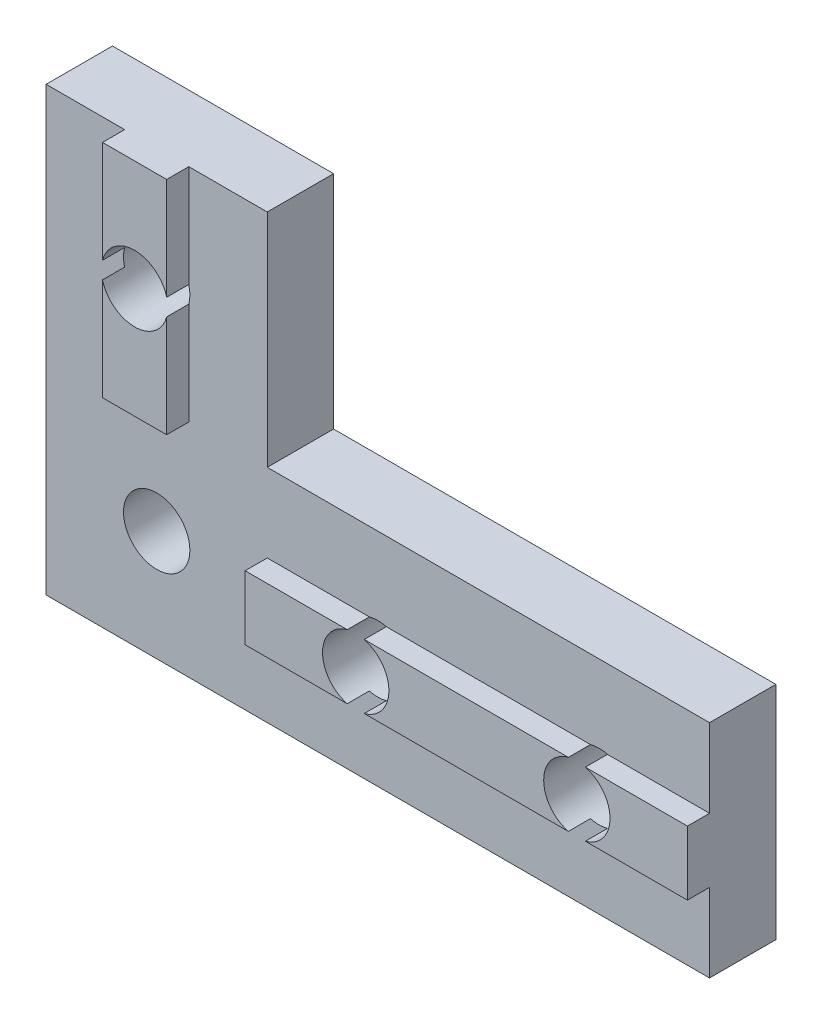
SolidWorks part; units mm, degrees
ref_plane "Front Plane" through (0, 0, 0) normal (0, 0, 1) x (1, 0, 0)
ref_plane "Top Plane" through (0, 0, 0) normal (0, 1, 0) x (1, 0, 0)
ref_plane "Right Plane" through (0, 0, 0) normal (1, 0, 0) x (0, 0, -1)
sketch "Esquisse1" plane through (0, 0, 0) normal (0, 0, 1) x (1, 0, 0)
  line L0 (0, 0) -> (30, 0)
  line L1 (30, 0) -> (30, 10)
  line L2 (30, 10) -> (10, 10)
  line L3 (10, 10) -> (10, 20)
  line L4 (10, 20) -> (0, 20)
  line L5 (0, 20) -> (0, 0)
  point P18 (5, 20)
  point P20 (30, 5)
  dimension "D2" = 20
  dimension "D1" = 10
  dimension "D8" = 30
extrude "Boss.-Extru.1" add sketch "Esquisse1" along normal blind 3
sketch "Esquisse2" plane through (0, 0, 3) normal (0, 0, 1) x (1, 0, 0)
  line L0 (10, 20) -> (0, 20) construction
  line L1 (6.45, 20) -> (3.55, 20)
  line L2 (6.45, 20) -> (6.45, 10)
  line L3 (6.45, 10) -> (3.55, 10)
  line L4 (3.55, 20) -> (3.55, 10)
  line L5 (30, 0) -> (30, 10) construction
  line L6 (30, 6.45) -> (10, 6.45)
  line L7 (30, 6.45) -> (30, 3.55)
  line L8 (30, 3.55) -> (10, 3.55)
  line L9 (10, 6.45) -> (10, 3.55)
  line L10 (30, 10) -> (10, 10) construction
  line L11 (10, 10) -> (10, 20) construction
  point P12 (5, 20)
  point P13 (5, 20)
  point P18 (30, 5)
  point P19 (30, 5)
  dimension "D1" = 2.9
extrude "Boss.-Extru.2" add sketch "Esquisse2" along normal blind 1
sketch "Esquisse3" plane through (0, 0, 0) normal (0, 0, -1) x (-1, 0, 0)
  line L0 (-10, 20) -> (0, 20) construction
  line L1 (-30, 0) -> (-30, 10) construction
  circle A0 centre (-25, 5) radius 1.5
  circle A1 centre (-15, 5) radius 1.5
  circle A2 centre (-5, 15) radius 1.5
  circle A3 centre (-5, 5) radius 1.5
  point P8 (0, 0)
  point P11 (-5, 20)
  point P14 (0, 0)
  point P15 (-30, 5)
  dimension "D1" = 3
  dimension "D2" = 5
  dimension "D3" = 5
  dimension "D4" = 10
extrude "Enlèv. mat.-Extru.1" cut sketch "Esquisse3" against normal through all
